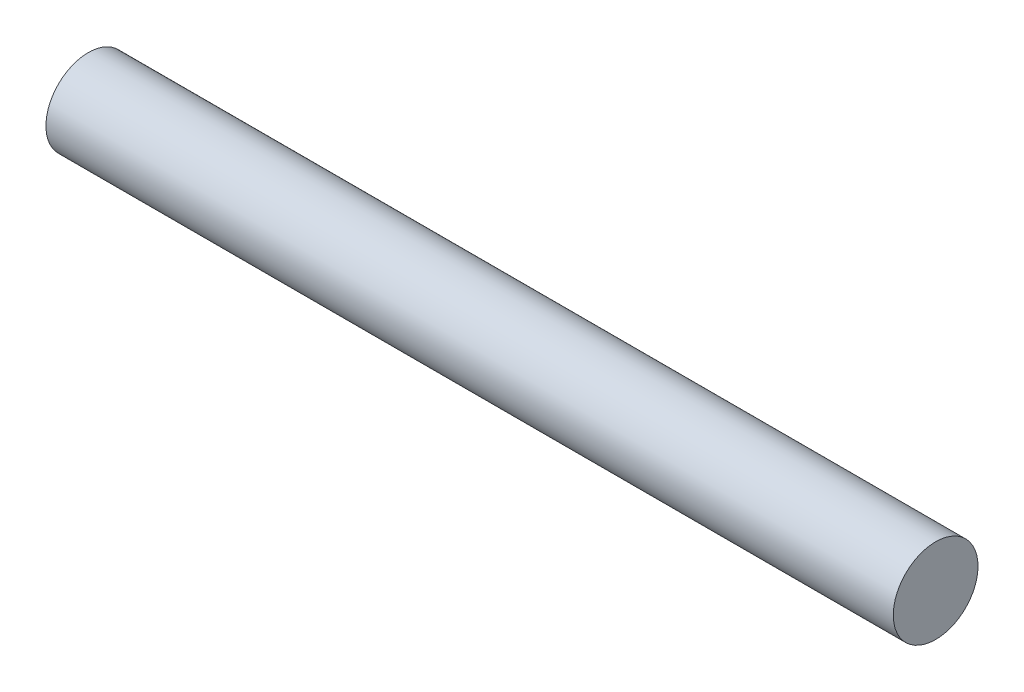
SolidWorks part; units mm, degrees
ref_plane "Front Plane" through (0, 0, 0) normal (0, 0, 1) x (1, 0, 0)
ref_plane "Top Plane" through (0, 0, 0) normal (0, 1, 0) x (1, 0, 0)
ref_plane "Right Plane" through (0, 0, 0) normal (1, 0, 0) x (0, 0, -1)
sketch "Sketch1" plane through (0, 0, 0) normal (1, 0, 0) x (0, 0, -1)
  circle A0 centre (0, 0) radius 15
  dimension "D1" = 30
extrude "Boss-Extrude1" add sketch "Sketch1" along normal blind 300
